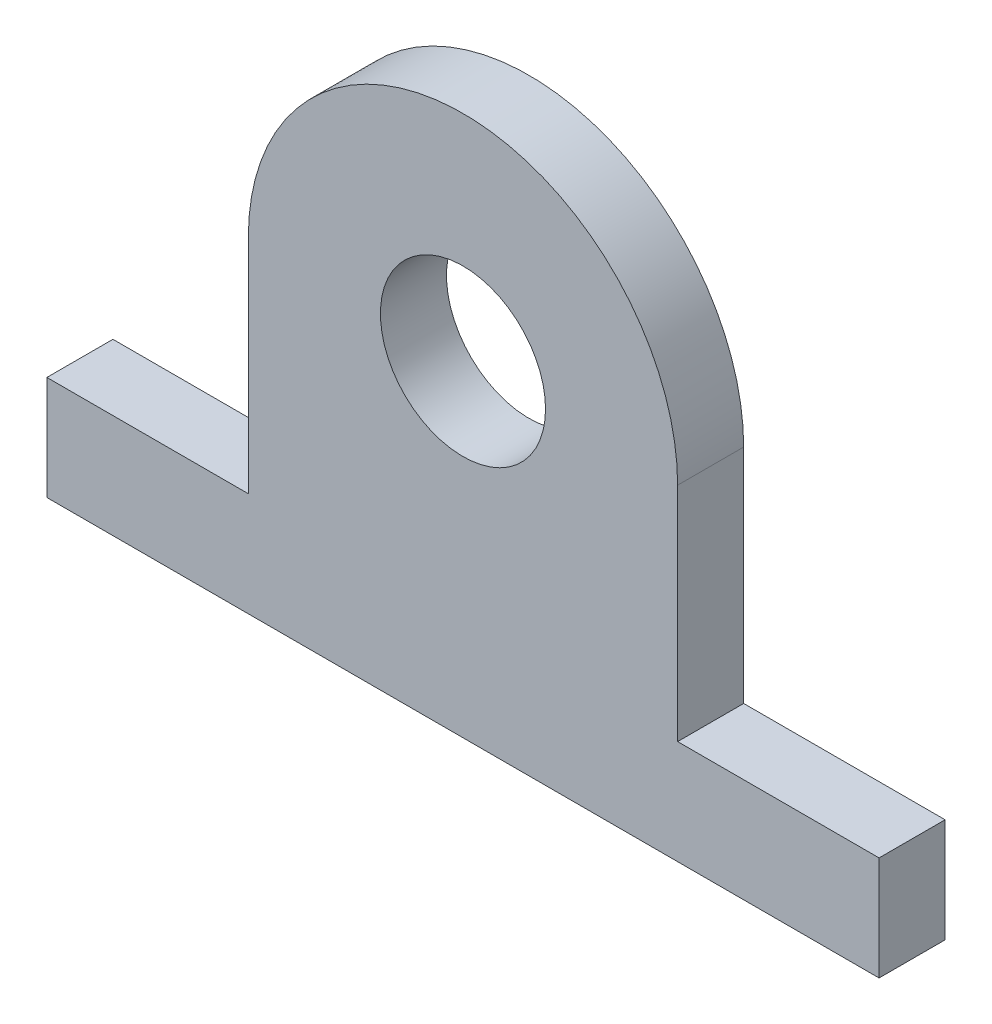
SolidWorks part; units mm, degrees
ref_plane "Front Plane" through (0, 0, 0) normal (0, 0, 1) x (1, 0, 0)
ref_plane "Top Plane" through (0, 0, 0) normal (0, 1, 0) x (1, 0, 0)
ref_plane "Right Plane" through (0, 0, 0) normal (1, 0, 0) x (0, 0, -1)
sketch "Sketch1" plane through (0, 0, 0) normal (0, 0, 1) x (1, 0, 0)
  line L0 (0, 0) -> (0, -31.35) construction
  line L1 (-40.005, -31.35) -> (40.005, -31.35)
  line L2 (-40.005, -31.35) -> (-40.005, -21.35)
  line L3 (-40.005, -21.35) -> (-20.6375, -21.35)
  line L4 (40.005, -31.35) -> (40.005, -21.35)
  line L5 (-40.005, -31.35) -> (40.005, -21.35) construction
  line L6 (-40.005, -21.35) -> (40.005, -31.35) construction
  line L7 (-20.6375, 0) -> (-20.6375, -21.35)
  line L8 (20.6375, 0) -> (20.6375, -21.35)
  line L9 (20.6375, -21.35) -> (40.005, -21.35)
  circle A0 centre (0, 0) radius 7.9375
  arc A1 (20.6375, 0) -> (-20.6375, 0) centre (0, 0) ccw
  circle A2 centre (0, 0) radius 20.6375 construction
  point P4 (0, -26.35)
  dimension "D3" = 21.35
  dimension "D1" = 15.875
  dimension "D2" = 12.7
  dimension "D4" = 10
  dimension "D5" = 80.01
extrude "Boss-Extrude1" add sketch "Sketch1" along normal blind 6.35
